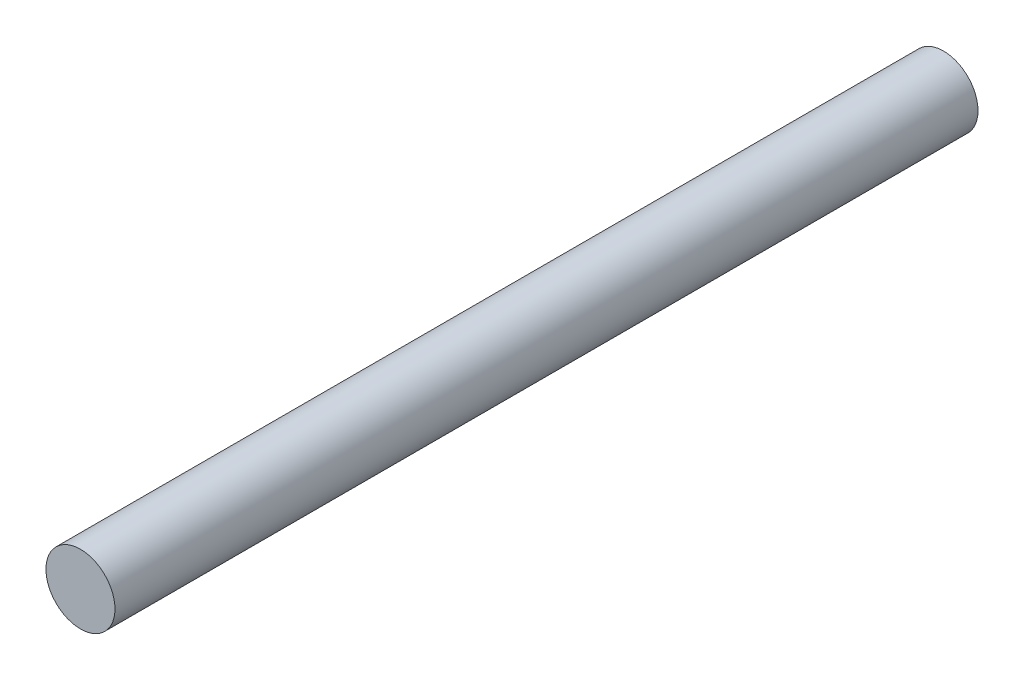
SolidWorks part; units mm, degrees
ref_plane "Front Plane" through (0, 0, 0) normal (0, 0, 1) x (1, 0, 0)
ref_plane "Top Plane" through (0, 0, 0) normal (0, 1, 0) x (1, 0, 0)
ref_plane "Right Plane" through (0, 0, 0) normal (1, 0, 0) x (0, 0, -1)
sketch "Sketch3" plane through (0, 0, 0) normal (0, 0, 1) x (1, 0, 0)
  circle A0 centre (0, 0) radius 2.54
  dimension "D1" = 5.08
extrude "Boss-Extrude2" add sketch "Sketch3" along normal blind 63.5
ref_plane "Plane1" through (12.7, 0, 0) normal (1, 0, 0) x (0, 0, -1)
sketch "Sketch4" plane through (12.7, 0, 0) normal (1, 0, 0) x (0, 0, -1)
  line L0 (-63.5, 2.54) -> (-63.5, -2.54) construction
  line L1 (-63.5, 0) -> (0, 0) construction
  circle A0 centre (-58.42, 0) radius 0.635
  point P7 (0, 0)
  dimension "D2" = 1.27
  dimension "D1" = 5.08
